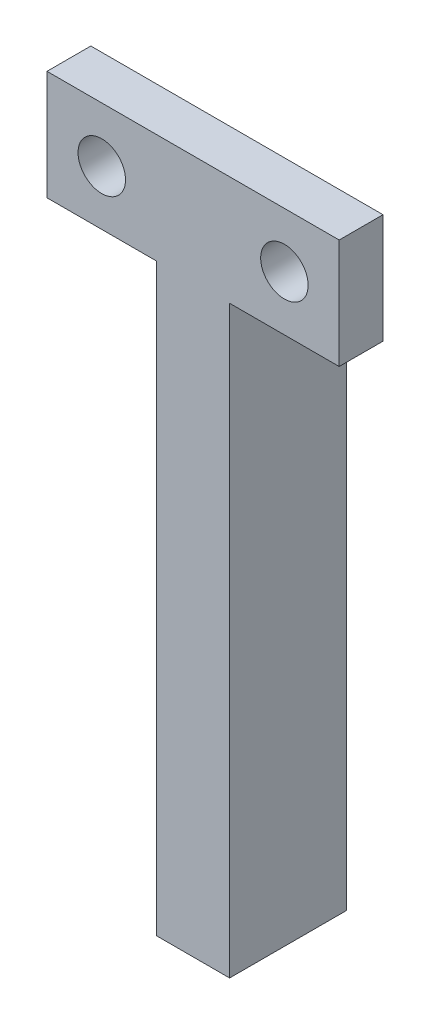
SolidWorks part; units mm, degrees
ref_plane "Front Plane" through (0, 0, 0) normal (0, 0, 1) x (1, 0, 0)
ref_plane "Top Plane" through (0, 0, 0) normal (0, 1, 0) x (1, 0, 0)
ref_plane "Right Plane" through (0, 0, 0) normal (1, 0, 0) x (0, 0, -1)
sketch "Sketch1" plane through (0, 0, 0) normal (0, 0, 1) x (1, 0, 0)
  line L0 (0, 0) -> (0, 40)
  line L1 (0, 40) -> (-7.5, 40)
  line L2 (-7.5, 40) -> (-7.5, 47.5)
  line L3 (-7.5, 47.5) -> (12.5, 47.5)
  line L4 (12.5, 47.5) -> (12.5, 40)
  line L5 (12.5, 40) -> (5, 40)
  line L6 (5, 40) -> (5, 0)
  line L7 (5, 0) -> (0, 0)
  circle A0 centre (-3.75, 43.75) radius 1.625
  circle A1 centre (8.75, 43.75) radius 1.625
  point P13 (12.5, 43.75)
  point P15 (-3.75, 40)
  point P17 (8.75, 40)
  dimension "D6" = 3.25
  dimension "D1" = 5
  dimension "D2" = 7.5
  dimension "D4" = 7.5
  dimension "D5" = 40
extrude "Boss-Extrude1" add sketch "Sketch1" along normal blind 3
sketch "Sketch3" plane through (0, 0, 0) normal (0, 0, -1) x (-1, 0, 0)
  line L1 (-5, 40) -> (0, 40)
  line L2 (-5, 40) -> (-5, 0)
  line L3 (-5, 0) -> (0, 0)
  line L4 (0, 40) -> (0, 0)
extrude "Boss-Extrude3" add sketch "Sketch3" along normal blind 5
